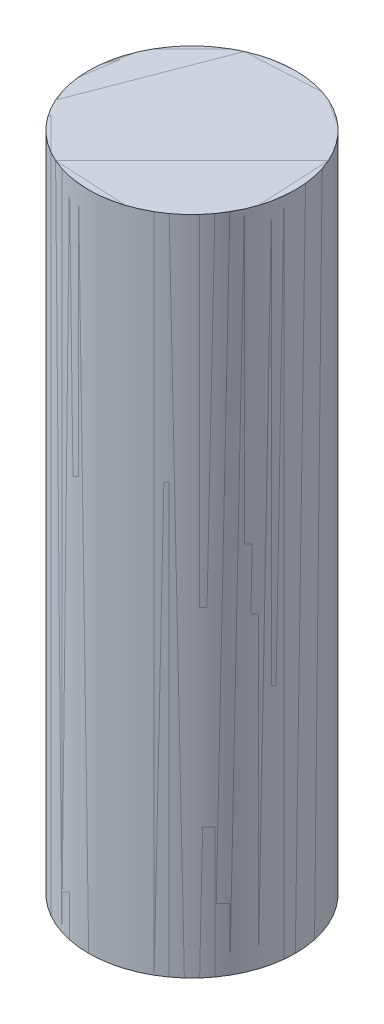
SolidWorks part; units mm, degrees
other "COLL.CYLINDER-Boss-Extrude2"
material "Nylon 101"
ref_plane "Front Plane" through (0, 0, 0) normal (0, 0, 1) x (1, 0, 0)
ref_plane "Top Plane" through (0, 0, 0) normal (0, 1, 0) x (1, 0, 0)
ref_plane "Right Plane" through (0, 0, 0) normal (1, 0, 0) x (0, 0, -1)
sketch "Sketch1" plane through (0, 0, 0) normal (0, 1, 0) x (1, 0, 0)
  circle A0 centre (0, 0) radius 12.5
  dimension "D1" = 25
extrude "Boss-Extrude1" add sketch "Sketch1" along normal blind 80
sketch "Sketch5" plane through (0, 0, 0) normal (0, -1, 0) x (-1, 0, 0)
  circle A0 centre (0, 0) radius 12.5
extrude "Boss-Extrude2" add sketch "Sketch5" against normal blind 80 separate body
